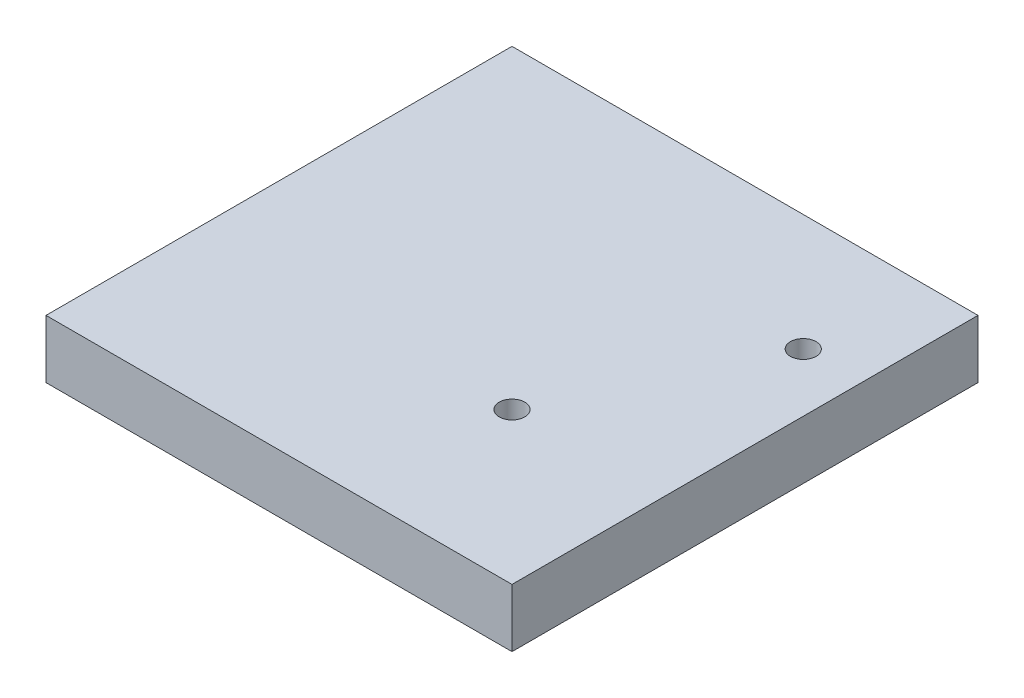
SolidWorks part; units mm, degrees
ref_plane "Front Plane" through (0, 0, 0) normal (0, 0, 1) x (1, 0, 0)
ref_plane "Top Plane" through (0, 0, 0) normal (0, 1, 0) x (1, 0, 0)
ref_plane "Right Plane" through (0, 0, 0) normal (1, 0, 0) x (0, 0, -1)
sketch "Sketch1" plane through (0, 0, 0) normal (0, 1, 0) x (1, 0, 0)
  line L1 (0, 0) -> (40, 0)
  line L2 (0, 0) -> (0, 40)
  line L3 (0, 40) -> (40, 40)
  line L4 (40, 0) -> (40, 40)
  circle A0 centre (27, 13) radius 1.1
  circle A1 centre (35, 30) radius 1.1
  dimension "D3" = 13
  dimension "D5" = 10
  dimension "D1" = 40
  dimension "D2" = 40
  dimension "D4" = 13
  dimension "D6" = 5
extrude "Boss-Extrude1" add sketch "Sketch1" along normal blind 5
